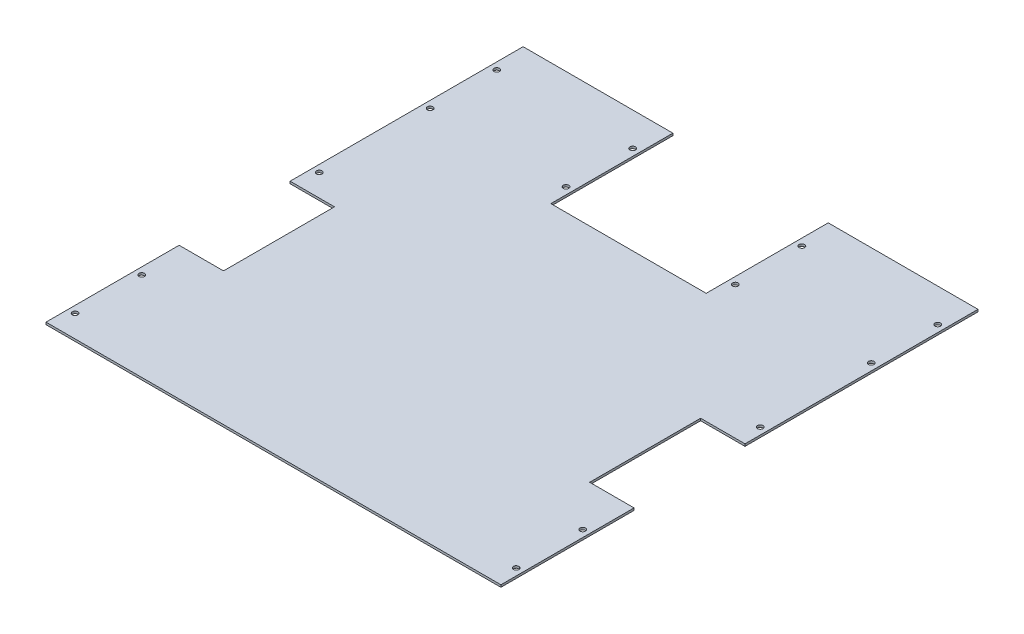
SolidWorks part; units mm, degrees
ref_plane "Front Plane" through (0, 0, 0) normal (0, 0, 1) x (1, 0, 0)
ref_plane "Top Plane" through (0, 0, 0) normal (0, 1, 0) x (1, 0, 0)
ref_plane "Right Plane" through (0, 0, 0) normal (1, 0, 0) x (0, 0, -1)
sketch "Sketch1" plane through (0, 0, 0) normal (0, 1, 0) x (1, 0, 0)
  line L0 (0, 279.4) -> (0, 546.1)
  line L1 (0, 0) -> (520.7, 0)
  line L2 (0, 0) -> (0, 152.4)
  line L3 (0, 546.1) -> (171.45, 546.1)
  line L4 (520.7, 0) -> (520.7, 152.4)
  line L5 (0, 152.4) -> (50.8, 152.4)
  line L7 (0, 279.4) -> (50.8, 279.4)
  line L8 (50.8, 152.4) -> (50.8, 279.4)
  line L9 (520.7, 279.4) -> (520.7, 546.1)
  line L10 (520.7, 152.4) -> (469.9, 152.4)
  line L12 (520.7, 279.4) -> (469.9, 279.4)
  line L13 (469.9, 152.4) -> (469.9, 279.4)
  line L14 (349.25, 546.1) -> (520.7, 546.1)
  line L16 (171.45, 546.1) -> (171.45, 406.4)
  line L17 (171.45, 406.4) -> (349.25, 406.4)
  line L18 (349.25, 546.1) -> (349.25, 406.4)
  dimension "D1" = 520.7
  dimension "D2" = 546.1
  dimension "D3" = 152.4
  dimension "D4" = 127
  dimension "D5" = 50.8
  dimension "D6" = 152.4
  dimension "D7" = 127
  dimension "D8" = 50.8
  dimension "D9" = 171.45
  dimension "D10" = 177.8
  dimension "D11" = 139.7
extrude "Boss-Extrude1" add sketch "Sketch1" along normal blind 2.54
sketch "Sketch2" plane through (0, 2.54, 0) normal (0, 1, 0) x (1, 0, 0)
  line L0 (171.45, 546.1) -> (0, 546.1) construction
  line L1 (0, 546.1) -> (0, 279.4) construction
  line L2 (260.35, 406.4) -> (260.35, 0) construction
  line L3 (349.25, 406.4) -> (171.45, 406.4) construction
  line L4 (0, 0) -> (520.7, 0) construction
  circle A0 centre (7.9375, 508) radius 3.175
  circle A1 centre (163.5125, 508) radius 3.175
  circle A2 centre (7.9375, 431.8) radius 3.175
  circle A3 centre (163.5125, 431.8) radius 3.175
  circle A4 centre (7.9375, 304.8) radius 3.175
  circle A5 centre (7.9375, 101.6) radius 3.175
  circle A6 centre (7.9375, 25.4) radius 3.175
  circle A7 centre (512.7625, 25.4) radius 3.175
  circle A8 centre (512.7625, 101.6) radius 3.175
  circle A9 centre (512.7625, 304.8) radius 3.175
  circle A10 centre (357.1875, 431.8) radius 3.175
  circle A11 centre (512.7625, 431.8) radius 3.175
  circle A12 centre (357.1875, 508) radius 3.175
  circle A13 centre (512.7625, 508) radius 3.175
  dimension "D1" = 6.35
  dimension "D3" = 6.35
  dimension "D8" = 6.35
  dimension "D10" = 6.35
  dimension "D12" = 6.35
  dimension "D2" = 38.1
  dimension "D4" = 38.1
  dimension "D5" = 155.575
  dimension "D6" = 7.9375
  dimension "D9" = 127
  dimension "D11" = 203.2
  dimension "D13" = 76.2
  dimension "D7" = 2
extrude "Cut-Extrude1" cut sketch "Sketch2" against normal through all
equation "\"D3@Sketch2\"=\"D1@Sketch2\""
equation "\"D4@Sketch2\"=\"D2@Sketch2\""
